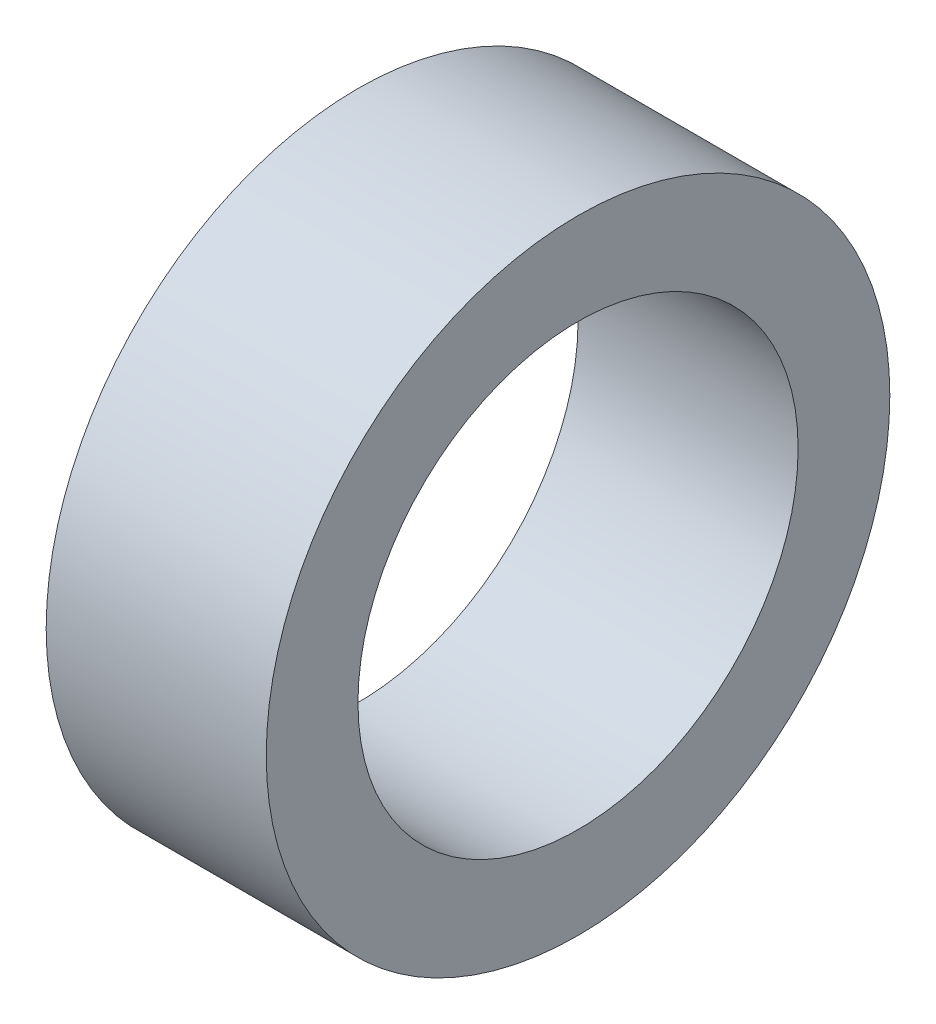
SolidWorks part; units mm, degrees
material "1.4305 (X8CrNiS18-9)"
ref_plane "Front Plane" through (0, 0, 0) normal (0, 0, 1) x (1, 0, 0)
ref_plane "Top Plane" through (0, 0, 0) normal (0, 1, 0) x (1, 0, 0)
ref_plane "Right Plane" through (0, 0, 0) normal (1, 0, 0) x (0, 0, -1)
ref_axis "Axis1" through (-88.99, 0, 0) along (1, 0, 0)
sketch "Sketch1" plane through (0, 0, 0) normal (0, 0, 1) x (1, 0, 0)
  line L0 (-88.99, 0) -> (88.99, 0) construction
  line L1 (0, 4.25) -> (3, 4.25)
  line L2 (0, 4.25) -> (0, 3)
  line L3 (0, 3) -> (3, 3)
  line L4 (3, 4.25) -> (3, 3)
  dimension "D1" = 6
  dimension "D2" = 8.5
  dimension "D3" = 3
revolve "Revolve1" add sketch "Sketch1" angle 360 about axis through (-88.99, 0, 0) along (1, 0, 0)
